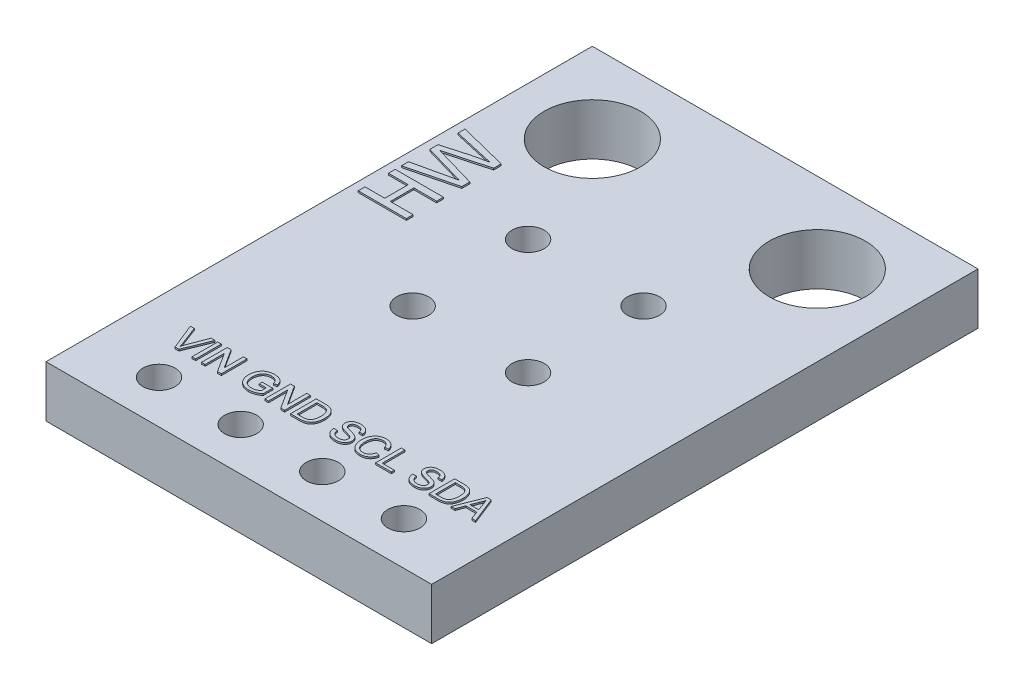
SolidWorks part; units mm, degrees
ref_plane "Спереди" through (0, 0, 0) normal (0, 0, 1) x (1, 0, 0)
ref_plane "Сверху" through (0, 0, 0) normal (0, 1, 0) x (1, 0, 0)
ref_plane "Справа" through (0, 0, 0) normal (1, 0, 0) x (0, 0, -1)
sketch "Эскиз2" plane through (0, 0, 0) normal (0, 1, 0) x (1, 0, 0)
  line L0 (-11.7073, 3.2889) -> (49988.2927, 3.2889) construction
  line L1 (-7.3568, 5.7889) -> (4.6432, 5.7889)
  line L2 (-7.3568, 5.7889) -> (-7.3568, -11.2111)
  line L3 (-7.3568, -11.2111) -> (4.6432, -11.2111)
  line L4 (4.6432, 5.7889) -> (4.6432, -11.2111)
  line L5 (-7.3568, -2.2111) -> (4.6432, -2.2111) construction
  line L6 (-3.1528, -0.415) -> (-1.3568, -2.2111) construction
  line L7 (-6.9691, -9.8738) -> (49993.0309, -9.8738) construction
  line L8 (-1.3568, -2.2111) -> (-1.3568, 0.3289) construction
  circle A0 centre (-4.8568, 3.2889) radius 1.5
  circle A1 centre (2.1432, 3.2889) radius 1.5
  circle A2 centre (-5.1768, -9.8738) radius 0.5
  circle A3 centre (-2.6368, -9.8738) radius 0.5
  circle A4 centre (-0.0968, -9.8738) radius 0.5
  circle A5 centre (2.4432, -9.8738) radius 0.5
  circle A6 centre (-1.3568, -2.2111) radius 2.54 construction
  circle A7 centre (-3.1528, -0.415) radius 0.5
  circle A8 centre (0.4393, -0.415) radius 0.5
  circle A9 centre (0.4393, -4.0071) radius 0.5
  circle A10 centre (-3.1528, -4.0071) radius 0.5
  point P26 (-7.3568, -2.7111)
  dimension "D6" = 3
  dimension "D7" = 3
  dimension "D8" = 1
  dimension "D9" = 1
  dimension "D10" = 1
  dimension "D11" = 1
  dimension "D12" = 2.54
  dimension "D13" = 2.54
  dimension "D14" = 2.54
  dimension "D15" = 2.2
  dimension "D16" = 1
  dimension "D4" = 5.08
  dimension "D1" = 12
  dimension "D2" = 17
  dimension "D3" = 2.5
  dimension "D5" = 0.5
extrude "Бобышка-Вытянуть1" add sketch "Эскиз2" along normal blind 1.6
sketch "Эскиз3" plane through (0, 1.6, 0) normal (0, 1, 0) x (1, 0, 0)
  line L0 (-5.5568, 2.7889) -> (-5.5568, -3.2111) construction
  line L1 (-7.3568, 5.7889) -> (-7.3568, -11.2111) construction
  line L2 (4.6432, 5.7889) -> (-7.3568, 5.7889) construction
  text T0 "VIN GND SCL SDA" font "Arial" height 0.8
  text T1 "HW" font "Arial" height 1.5
  dimension "D1" = 1.8
  dimension "D2" = 3
  dimension "D3" = 9
extrude "Бобышка-Вытянуть2" add sketch "Эскиз3" along normal blind 0.05
sketch "Эскиз4" plane through (0, 0, 0) normal (0, -1, 0) x (1, 0, 0)
  line L0 (4.2432, 4.2774) -> (4.2432, -1.2048) construction
  line L1 (4.6432, 11.2111) -> (4.6432, -5.7889) construction
  text T0 "HW-691" font "Arial" height 1
  dimension "D1" = 0.4
extrude "Бобышка-Вытянуть3" add sketch "Эскиз4" along normal blind 0.01
